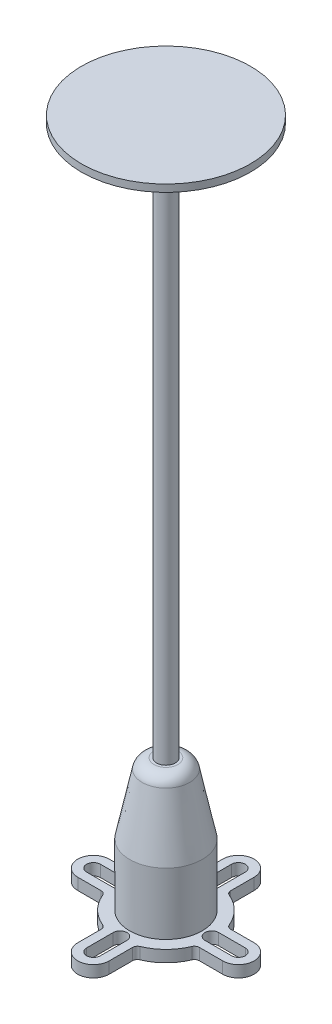
SolidWorks part; units mm, degrees
material "GPS İSKELET"
ref_plane "Ön Düzlem" through (0, 0, 0) normal (0, 0, 1) x (1, 0, 0)
ref_plane "Üst Düzlem" through (0, 0, 0) normal (0, 1, 0) x (1, 0, 0)
ref_plane "Sağ Düzlem" through (0, 0, 0) normal (1, 0, 0) x (0, 0, -1)
sketch "Sketch1" plane through (0, 0, 0) normal (0, 1, 0) x (1, 0, 0)
  line L0 (-340.0605, 0) -> (16662.9662, 0) construction
  line L1 (0, -340.0605) -> (0, 16662.9662) construction
  line L2 (-15, 3.25) -> (-9.4571, 3.25)
  line L3 (-15, -3.25) -> (-9.4571, -3.25)
  line L4 (-15, 0) -> (-9.5, 0) construction
  line L5 (-15, 1.42) -> (-9.5, 1.42)
  line L6 (-15, -1.42) -> (-9.5, -1.42)
  line L7 (3.25, 15) -> (3.25, 9.4571)
  line L8 (-3.25, 15) -> (-3.25, 9.4571)
  line L9 (0, 15) -> (0, 9.5) construction
  line L10 (1.42, 15) -> (1.42, 9.5)
  line L11 (-1.42, 15) -> (-1.42, 9.5)
  line L12 (15, -3.25) -> (9.4571, -3.25)
  line L13 (15, 3.25) -> (9.4571, 3.25)
  line L14 (15, 0) -> (9.5, 0) construction
  line L15 (15, -1.42) -> (9.5, -1.42)
  line L16 (15, 1.42) -> (9.5, 1.42)
  line L17 (-3.25, -15) -> (-3.25, -9.4571)
  line L18 (3.25, -15) -> (3.25, -9.4571)
  line L19 (0, -15) -> (0, -9.5) construction
  line L20 (-1.42, -15) -> (-1.42, -9.5)
  line L21 (1.42, -15) -> (1.42, -9.5)
  arc A0 (-15, 3.25) -> (-15, -3.25) centre (-15, 0) ccw
  arc A1 (-9.4571, -3.25) -> (-3.25, -9.4571) centre (0, 0) ccw
  arc A2 (-15, 1.42) -> (-15, -1.42) centre (-15, 0) ccw
  arc A3 (-9.5, -1.42) -> (-9.5, 1.42) centre (-9.5, 0) ccw
  arc A4 (3.25, 15) -> (-3.25, 15) centre (0, 15) ccw
  arc A5 (1.42, 15) -> (-1.42, 15) centre (0, 15) ccw
  arc A6 (-1.42, 9.5) -> (1.42, 9.5) centre (0, 9.5) ccw
  arc A7 (15, -3.25) -> (15, 3.25) centre (15, 0) ccw
  arc A8 (15, -1.42) -> (15, 1.42) centre (15, 0) ccw
  arc A9 (9.5, 1.42) -> (9.5, -1.42) centre (9.5, 0) ccw
  arc A10 (-3.25, -15) -> (3.25, -15) centre (0, -15) ccw
  arc A11 (-1.42, -15) -> (1.42, -15) centre (0, -15) ccw
  arc A12 (1.42, -9.5) -> (-1.42, -9.5) centre (0, -9.5) ccw
  arc A13 (-3.25, 9.4571) -> (-9.4571, 3.25) centre (0, 0) ccw
  arc A15 (9.4571, 3.25) -> (3.25, 9.4571) centre (0, 0) ccw
  arc A17 (3.25, -9.4571) -> (9.4571, -3.25) centre (0, 0) ccw
  point P6 (-12.25, 0)
  point P21 (0, 12.25)
  point P32 (12.25, 0)
  point P43 (0, -12.25)
  dimension "D1" = 6.5
  dimension "D3" = 20
  dimension "D4" = 1.42
  dimension "D2" = 15
  dimension "D5" = 5.5
  dimension "D6" = 4
extrude "Boss-Extrude1" add sketch "Sketch1" along normal blind 2.4
fillet "Fillet1" radius 1 8 edges at (9.4571, 1.2, -3.25) (3.25, 1.2, -9.4571) (-3.25, 1.2, -9.4571) (-9.4571, 1.2, -3.25) (-9.4571, 1.2, 3.25) (-3.25, 1.2, 9.4571) (9.4571, 1.2, 3.25) (3.25, 1.2, 9.4571)
sketch "Sketch2" plane through (0, 0, 0) normal (0, 0, 1) x (1, 0, 0)
  line L0 (0, 0) -> (0, 2.4) construction
  line L1 (3.25, 2.4) -> (-3.25, 2.4) construction
  line L2 (0, 2.4) -> (0, 29.7) construction
  line L3 (1.925, 29.7) -> (2.4643, 29.7)
  line L4 (4.9124, 27.7065) -> (7.5, 15.2)
  line L5 (7.5, 15.2) -> (7.5, 2.4)
  line L6 (9.2235, 2.4) -> (3.8636, 2.4) construction
  line L7 (7.5, 2.4) -> (5.625, 2.4)
  line L8 (5.625, 2.4) -> (5.625, 15.2)
  line L9 (5.625, 15.2) -> (3.4049, 26.1948)
  line L11 (0, 28.2) -> (0, 29.7) construction
  line L12 (1.925, 29.7) -> (1.925, 28.0039)
  arc A0 (3.4049, 26.1948) -> (1.925, 28.0039) centre (0.9544, 25.7) ccw
  arc A1 (2.4643, 29.7) -> (4.9124, 27.7065) centre (2.4643, 27.2) cw
  point P17 (3, 28.2)
  point P20 (4.5, 29.7)
  dimension "D7" = 2.5
  dimension "D1" = 7.5
  dimension "D2" = 11.25
  dimension "D3" = 14.5
  dimension "D4" = 1.5
  dimension "D5" = 9
  dimension "D6" = 6
  dimension "D8" = 27.3
  dimension "D9" = 3.85
revolve "Revolve1" add sketch "Sketch2" angle 360 about L2
sketch "Sketch3" plane through (0, 2.4, 0) normal (0, 1, 0) x (1, 0, 0)
  circle A0 centre (0, 0) radius 1.9225
  dimension "D1" = 3.845
extrude "Boss-Extrude2" add sketch "Sketch3" along normal blind 141
sketch "Sketch4" plane through (0, 0, 0) normal (1, 0, 0) x (0, 0, -1)
  line L0 (0, 143.4) -> (0, 135.6) construction
  line L1 (1.9225, 143.4) -> (-1.9225, 143.4) construction
  line L2 (6.9226, 142.4) -> (3.2309, 136.0058)
  line L5 (8.6547, 143.4) -> (17.5, 143.4)
  line L6 (17.5, 143.4) -> (17.5, 144.9)
  line L7 (17.5, 144.9) -> (0, 144.9)
  line L8 (0, 144.9) -> (0, 143.4)
  line L9 (0, 143.4) -> (1.9225, 143.4)
  line L11 (2.5381, 135.6058) -> (1.9225, 135.6058)
  line L12 (1.9225, 2.4) -> (1.9225, 143.4) construction
  line L13 (1.9225, 135.6058) -> (1.9225, 143.4)
  arc A0 (6.9226, 142.4) -> (8.6547, 143.4) centre (8.6547, 141.4) cw
  arc A1 (3.2309, 136.0058) -> (2.5381, 135.6058) centre (2.5381, 136.4058) cw
  point P17 (7.5, 143.4)
  point P20 (3, 135.6058)
  dimension "D8" = 2
  dimension "D9" = 0.8
  dimension "D1" = 7.8
  dimension "D2" = 1.5
  dimension "D3" = 35
  dimension "D4" = 1.5
  dimension "D5" = 3
  dimension "D6" = 30
  dimension "D7" = 15
revolve "Revolve2" add sketch "Sketch4" angle 360 about L0
sketch "Çizim1" plane through (0, 143.4, 0) normal (0, -1, 0) x (1, 0, 0)
  arc A0 (-2.1228, 9.9839) -> (8.986, 4.1699) centre (0.5246, 1.5225) cw construction
  text T0 "E A G" font "Gill Sans Ultra Bold" height 3.5
extrude "Kes-Ekstrüzyon1" cut sketch "Çizim1" against normal blind 0.06
